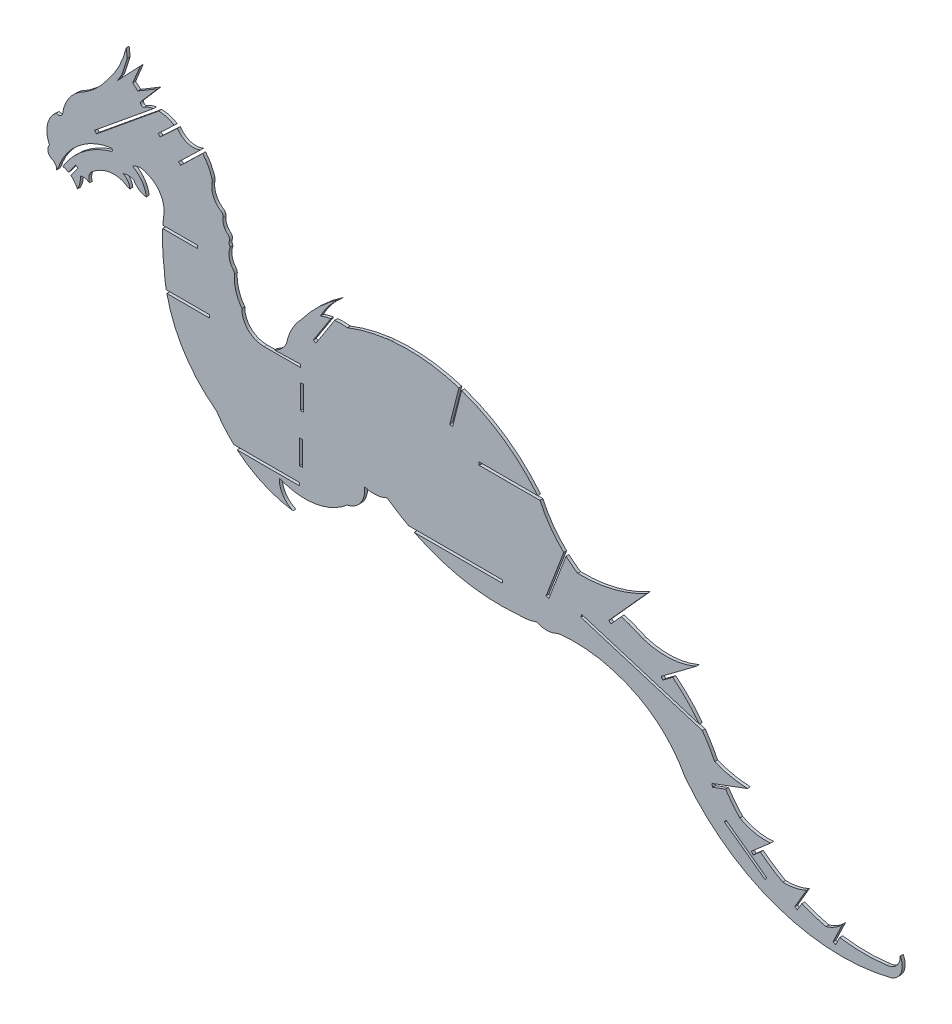
SolidWorks part; units mm, degrees
ref_plane "Front Plane" through (0, 0, 0) normal (0, 0, 1) x (1, 0, 0)
ref_plane "Top Plane" through (0, 0, 0) normal (0, 1, 0) x (1, 0, 0)
ref_plane "Right Plane" through (0, 0, 0) normal (1, 0, 0) x (0, 0, -1)
sketch "Sketch1" plane through (0, 0, 0) normal (0, 0, 1) x (1, 0, 0)
  line L13 (85.913, 218.9763) -> (74.3649, 207.8002)
  line L14 (84.8531, 220.0714) -> (73.305, 208.8953)
  line L15 (74.3649, 207.8002) -> (73.305, 208.8953)
  line L16 (72.6706, 223.8437) -> (63.5101, 215.2597)
  line L17 (70.9424, 224.3128) -> (62.468, 216.3718)
  line L18 (63.5101, 215.2597) -> (62.468, 216.3718)
  line L19 (53.5004, 226.3834) -> (62.3378, 236.6274)
  line L20 (71.6285, 224.9557) -> (62.468, 216.3718) construction
  line L21 (62.3378, 236.6274) -> (51.8511, 230.3661)
  line L22 (51.8511, 230.3661) -> (49.1514, 232.6951)
  line L23 (49.1514, 232.6951) -> (53.1855, 242.4071)
  line L24 (53.1855, 242.4071) -> (41.0252, 229.6436)
  line L25 (41.0252, 229.6436) -> (43.4334, 233.4967)
  line L26 (43.4334, 233.4967) -> (46.2631, 242.4071)
  line L27 (46.2631, 242.4071) -> (45.7814, 247.0429)
  line L33 (29.66, 200.589) -> (66.6896, 230.8776) construction
  line L49 (188.6151, 187.6952) -> (169.1948, 168.6314) construction
  line L51 (182.7923, 183.0471) -> (168.661, 169.1752)
  line L54 (185.2534, 183.3275) -> (169.7286, 168.0877)
  line L56 (168.661, 169.1752) -> (169.7286, 168.0877)
  line L57 (157.4617, 182.5358) -> (144.7171, 162.7649) construction
  line L58 (153.3021, 177.4895) -> (144.0766, 163.1777)
  line L59 (155.2936, 177.766) -> (145.3576, 162.352)
  line L60 (30.1424, 199.9991) -> (62.8231, 226.7305)
  line L61 (144.0766, 163.1777) -> (145.3576, 162.352)
  line L62 (188.0813, 188.239) -> (168.661, 169.1752) construction
  line L63 (158.1021, 182.123) -> (145.3576, 162.352) construction
  line L64 (156.8212, 182.9487) -> (144.0766, 163.1777) construction
  line L65 (189.1489, 187.1514) -> (169.7286, 168.0877) construction
  line L66 (29.1775, 201.1788) -> (60.1503, 226.5131)
  line L67 (30.1424, 199.9991) -> (29.1775, 201.1788)
  line L68 (30.1424, 199.9991) -> (67.1721, 230.2877) construction
  line L69 (29.1775, 201.1788) -> (66.2072, 231.4674) construction
  line L75 (16.6636, 174.3293) -> (20.4232, 179.4683)
  line L76 (15.3952, 175.1766) -> (19.1932, 180.3682)
  line L78 (20.4232, 179.4683) -> (19.1932, 180.3682)
  arc A0 (12.4112, 176.3386) -> (15.3952, 175.1766) centre (9.9945, 165.7194) cw
  arc A1 (20.0703, 169.8527) -> (21.6539, 176.5827) centre (9.8643, 175.8054) ccw
  arc A2 (21.6539, 176.5827) -> (26.4044, 175.8054) centre (23.3346, 171.949) cw
  arc A3 (26.4044, 175.8054) -> (27.2905, 181.1096) centre (31.4656, 177.686) cw
  arc A4 (27.2905, 181.1096) -> (35.949, 185.8295) centre (40.6259, 166.9481) cw
  arc A5 (35.949, 185.8295) -> (44.5288, 185.127) centre (39.1948, 172.7256) cw
  arc A6 (44.5288, 185.127) -> (47.6647, 183.6586) centre (51.8511, 196.6811) ccw
  arc A7 (47.6647, 183.6586) -> (44.1325, 188.8887) centre (41.5045, 183.3061) ccw
  arc A8 (44.1325, 188.8887) -> (49.7201, 188.8772) centre (46.9113, 181.6231) cw
  arc A9 (49.7201, 188.8772) -> (56.2646, 184.3098) centre (57.356, 192.8459) ccw
  arc A10 (56.2646, 184.3098) -> (49.1514, 194.7266) centre (42.906, 182.8248) ccw
  arc A11 (49.1514, 194.7266) -> (56.2715, 195.3335) centre (53.1855, 189.4687) cw
  arc A12 (56.2715, 195.3335) -> (65.6673, 182.2891) centre (52.257, 182.5358) cw
  arc A13 (65.6673, 182.2891) -> (65.646, 182.0044) centre (63.1277, 182.3359) cw
  arc A14 (65.7315, 155.9537) -> (70.314, 135.1914) centre (133.3951, 160.0009) ccw
  arc A15 (182.8341, 110.7237) -> (251.5533, 92.003) centre (242.2428, 193.3123) ccw
  arc A16 (161.9029, 96.9961) -> (163.2492, 97.3465) centre (159.7329, 108.0948) ccw
  arc A17 (170.8985, 109.8892) -> (182.8341, 110.7237) centre (175.8491, 124.8557) ccw
  arc A18 (445.4257, 29.3719) -> (452.4535, 37.0347) centre (444.9751, 36.8392) ccw
  arc A19 (452.4535, 37.0347) -> (447.9208, 24.8241) centre (444.8895, 32.896) cw
  arc A23 (261.361, 93.4868) -> (270.0689, 92.8939) centre (266.514, 104.9258) ccw
  arc A24 (272.556, 93.9304) -> (314.8204, 86.2928) centre (281.4797, 22.553) cw
  arc A25 (314.8204, 86.2928) -> (339.3161, 61.996) centre (287.7099, 34.4638) cw
  arc A26 (339.3161, 61.996) -> (447.9208, 24.8241) centre (421.7648, 125.6448) ccw
  arc A28 (445.4257, 29.3719) -> (361.4817, 65.9392) centre (433.7482, 117.1995) cw
  arc A29 (295.5346, 120.6114) -> (296.0785, 120.4577) centre (296.4931, 122.9637) ccw
  arc A30 (287.5207, 123.6481) -> (263.1364, 149.7627) centre (314.575, 173.3516) cw
  arc A31 (263.1364, 149.7627) -> (185.2534, 183.3275) centre (193.9218, 96.3002) ccw
  arc A32 (161.9029, 177.6862) -> (155.2936, 177.766) centre (158.253, 149.1443) ccw
  arc A33 (129.9784, 154.4832) -> (114.0338, 147.9574) centre (118.2489, 160.4005) cw
  arc A34 (114.0338, 147.9574) -> (106.5299, 158.7224) centre (117.5806, 158.4275) cw
  arc A35 (106.5299, 158.7224) -> (102.5636, 172.3071) centre (123.2009, 170.9612) cw
  arc A36 (101.9536, 174.13) -> (100.3802, 183.4958) centre (108.899, 180.1119) cw
  arc A37 (100.3802, 183.4958) -> (99.9418, 186.1014) centre (102.74, 185.2325) cw
  arc A38 (90.9092, 208.4497) -> (90.8696, 209.6659) centre (88.4246, 208.9777) ccw
  arc A39 (95.4624, 197.6442) -> (90.9092, 208.4497) centre (100.9454, 206.3167) cw
  arc A40 (90.8696, 209.6659) -> (85.913, 218.9763) centre (67.0577, 202.9636) ccw
  arc A41 (84.8531, 220.0714) -> (72.6706, 223.8437) centre (80.9007, 228.8651) cw
  arc A42 (70.9424, 224.3128) -> (62.8231, 226.7305) centre (62.7145, 211.5233) ccw
  arc A43 (55.5843, 224.9557) -> (53.5004, 226.3834) centre (54.5423, 225.6696) cw
  arc A44 (45.7814, 247.0429) -> (35.949, 227.5413) centre (-0.6105, 258.2036) cw
  arc A45 (35.949, 227.5413) -> (20.6241, 214.0554) centre (0.5756, 252.288) cw
  arc A46 (20.6241, 214.0554) -> (12.4112, 200.9147) centre (32.5604, 197.4584) ccw
  arc A47 (12.4112, 200.9147) -> (9.042, 198.9031) centre (10.1268, 200.9135) cw
  arc A48 (9.042, 198.9031) -> (5.4551, 182.6164) centre (17.1859, 188.5712) ccw
  arc A49 (5.4551, 182.6164) -> (7.0761, 176.5827) centre (8.3888, 180.1699) ccw
  arc A50 (7.0761, 176.5827) -> (9.1559, 173.0992) centre (5.7188, 173.4097) cw
  arc A51 (9.1559, 173.0992) -> (10.7671, 176.5827) centre (1.9369, 178.5526) ccw
  arc A52 (163.2492, 97.3465) -> (170.8985, 109.8892) centre (159.7329, 108.0948) ccw
  arc A53 (126.1618, 91.5175) -> (161.9029, 96.9961) centre (139.6981, 122.5329) ccw
  arc A54 (251.5533, 92.003) -> (261.361, 93.4868) centre (252.5143, 118.8054) ccw
  arc A55 (270.0689, 92.8939) -> (272.556, 93.9304) centre (266.514, 104.9258) ccw
  arc A56 (153.3021, 177.4895) -> (147.8071, 175.9555) centre (158.253, 149.1443) ccw
  arc A57 (182.7923, 183.0471) -> (161.9029, 177.6862) centre (193.9218, 96.3002) ccw
  arc A58 (10.7671, 176.5827) -> (37.5404, 197.4595) centre (43.0104, 162.8387) cw
  arc A59 (37.5404, 197.4595) -> (38.2537, 196.0719) centre (37.6686, 196.6483) cw
  arc A60 (38.2537, 196.0719) -> (12.4112, 176.3386) centre (50.3099, 153.495) ccw
  arc A61 (16.6636, 174.3293) -> (20.0703, 169.8527) centre (9.9945, 165.7194) cw
  arc A62 (65.646, 182.0044) -> (65.0583, 176.1999) centre (162.201, 169.2959) ccw
  arc A63 (64.9437, 164.2568) -> (65.7315, 155.9537) centre (162.201, 169.2959) ccw
  arc A64 (102.5636, 172.3071) -> (101.9536, 174.13) centre (100.029, 172.4724) ccw
  arc A65 (65.0583, 176.1999) -> (64.9437, 164.2568) centre (162.201, 169.2959) ccw
  arc A66 (99.9418, 186.1014) -> (99.1107, 188.8317) centre (97.516, 186.8546) ccw
  arc A67 (70.314, 135.1914) -> (73.526, 128.2136) centre (133.3951, 160.0009) ccw
  arc A68 (73.526, 128.2136) -> (78.3629, 120.4256) centre (133.3951, 160.0009) ccw
  arc A69 (78.3629, 120.4256) -> (86.4403, 111.1133) centre (133.3951, 160.0009) ccw
  arc A70 (86.4403, 111.1133) -> (93.1568, 105.4516) centre (133.3951, 160.0009) ccw
  arc A73 (295.5346, 120.6114) -> (287.9072, 123.4777) centre (239.5785, -16.7097) ccw
  arc A74 (287.9072, 123.4777) -> (287.5207, 123.6481) centre (288.735, 125.879) cw
  arc A75 (60.1503, 226.5131) -> (55.5843, 224.9557) centre (62.7145, 211.5233) ccw
  arc A76 (361.4817, 65.9392) -> (355.3136, 75.9918) centre (433.7482, 117.1995) cw
  arc A77 (137.7135, 169.2959) -> (158.253, 188.8317) centre (205.9089, 118.162) cw
  arc A78 (158.253, 188.8317) -> (147.8071, 175.9555) centre (185.6114, 155.9616) ccw
  arc A79 (99.1107, 188.8317) -> (96.6201, 195.1422) centre (103.4255, 194.1813) cw
  arc A80 (95.4624, 197.6442) -> (96.6201, 195.1422) centre (94.1051, 195.4973) cw
  arc A81 (296.0785, 120.4577) -> (355.3136, 75.9918) centre (282.9903, 41.3344) cw
  arc A82 (137.7135, 169.2959) -> (129.9784, 154.4832) centre (158.253, 149.1443) ccw
  arc A83 (93.1568, 105.4516) -> (133.3951, 80.0979) centre (141.151, 137.0147) ccw
  arc A84 (133.3951, 80.0979) -> (126.1618, 91.5175) centre (138.1529, 91.1122) cw
  point P60 (287.71, 123.5456)
  point P75 (106.4494, 191.8735)
  point P90 (91.9787, 207.5822)
  point P91 (85.8872, 203.0521)
  point P136 (164.6579, 97.7541)
  point P137 (151.9566, 109.3259)
  point P142 (123.8865, 90.8069)
  point P143 (131.5718, 107.0888)
  point P144 (122.5084, 91.4575)
  point P145 (130.1936, 107.7393)
  point P150 (241.3162, 93.1293)
  point P151 (251.1656, 111.671)
  point P152 (239.9703, 93.8443)
  point P153 (249.8198, 112.386)
  point P158 (270.5568, 91.3637)
  point P159 (265.469, 107.3203)
  point P160 (269.1048, 90.9007)
  point P161 (264.017, 106.8573)
  point P198 (15.578, 174.1358)
  point P199 (19.8082, 179.9183)
  point P200 (16.193, 173.6859)
  point P202 (14.963, 174.5857)
  point P210 (63.6959, 166.7845)
  point P211 (94.3235, 178.4306)
  point P231 (101.2609, 99.9132)
  point P232 (101.2609, 106.2632)
  point P235 (93.1199, 104.9862)
  point P236 (93.6225, 111.3162)
  point P239 (86.3932, 110.4968)
  point P240 (86.8776, 116.8283)
  point P243 (78.1854, 119.9829)
  point P244 (80.5491, 125.8766)
  point P247 (73.2876, 127.7593)
  point P248 (76.1666, 133.2444)
  point P251 (70.0194, 134.7217)
  point P252 (73.334, 140.0066)
  point P255 (67.1082, 144.2075)
  point P256 (71.8777, 148.3139)
  point P259 (66.0068, 151.6009)
  point P260 (70.2987, 156.2808)
  point P263 (65.3242, 160.5131)
  point P264 (71.0012, 163.5977)
  point P265 (64.2375, 165.36)
  point P266 (94.8652, 177.0061)
  point P267 (64.8673, 168.7878)
  point P268 (70.723, 171.6385)
  point P271 (64.7168, 175.6756)
  point P272 (70.283, 178.3947)
  point P275 (64.6704, 181.0332)
  point P276 (70.3416, 184.2665)
  point P301 (295.3884, 121.098)
  point P302 (295.0266, 120.6245)
  point P305 (305.7328, 115.9997)
  point P306 (434.7823, 117.834)
  point P307 (296.6449, 120.1538)
  point P308 (450.936, 28.713)
  point P309 (304.9899, 116.6907)
  point P310 (304.4572, 115.9935)
  point P311 (354.6735, 75.5721)
  point P312 (239.5785, -16.7097)
  point P313 (305.3928, 115.3177)
  point P314 (239.5785, -16.7097)
  point P327 (296.3516, 119.4504)
  point P328 (239.5785, -16.7097)
  point P329 (287.4626, 122.8248)
  point P330 (298.9702, 124.191)
  point P331 (294.7489, 119.0435)
  point P332 (309.5956, 122.086)
  point P333 (303.3169, 114.1841)
  point P334 (300.1486, 123.2246)
  point P335 (295.9273, 118.0771)
  point P336 (310.7887, 121.1379)
  point P337 (304.5101, 113.236)
  point P338 (323.9026, 122.7437)
  point P339 (308.7162, 107.8646)
  point P340 (336.2019, 120.1065)
  point P341 (320.6027, 104.9604)
  point P342 (352.8142, 116.9997)
  point P343 (330.7576, 95.3744)
  point P344 (364.3369, 112.5519)
  point P345 (337.296, 83.9421)
  point P346 (373.3591, 103.5516)
  point P347 (349.2999, 75.3797)
  point P348 (380.3752, 98.2442)
  point P349 (359.4005, 62.3807)
  point P350 (324.9692, 121.6551)
  point P351 (309.7827, 106.776)
  point P352 (337.2635, 119.0131)
  point P353 (321.6643, 103.867)
  point P354 (353.8812, 115.9115)
  point P355 (331.8246, 94.2862)
  point P356 (365.4445, 111.5051)
  point P357 (338.4036, 82.8953)
  point P358 (374.518, 102.5619)
  point P359 (350.4588, 74.39)
  point P360 (381.6907, 97.4748)
  point P361 (360.716, 61.6113)
  dimension "D18" = 2.54
  dimension "D19" = 2.54
  dimension "D20" = 2.54
  dimension "D21" = 2.54
  dimension "D4" = 2.54
  dimension "D22" = 2.54
  dimension "D2" = 1.524
  dimension "D3" = 1.524
  dimension "D12" = 0.762
  dimension "D13" = 0.762
  dimension "D14" = 0.762
  dimension "D15" = 0.762
  dimension "D16" = 0.762
  dimension "D17" = 0.762
extrude "Boss-Extrude1" add sketch "Sketch1" along normal blind 1.524
sketch "Sketch2" plane through (0, 0, 1.524) normal (0, 0, 1) x (1, 0, 0)
  line L0 (64.0284, 147.4046) -> (89.4284, 147.4046)
  line L1 (64.0284, 174.349) -> (83.0784, 174.349)
  line L2 (64.0284, 174.349) -> (64.0284, 175.873)
  line L3 (64.0284, 175.873) -> (83.0784, 175.873)
  line L4 (83.0784, 174.349) -> (83.0784, 175.873)
  line L5 (64.0284, 145.8806) -> (64.0284, 147.4046)
  line L6 (64.0284, 145.8806) -> (89.4284, 145.8806)
  line L7 (89.4284, 145.8806) -> (89.4284, 147.4046)
extrude "Cut-Extrude1" cut sketch "Sketch2" against normal blind 2.54
sketch "Sketch3" plane through (0, 0, 1.524) normal (0, 0, 1) x (1, 0, 0)
  line L0 (118.2489, 147.2629) -> (137.2989, 147.2629)
  line L1 (137.2989, 147.2629) -> (137.2989, 148.7869)
  line L2 (137.2989, 148.7869) -> (118.2489, 148.2418)
  line L3 (118.2489, 148.2418) -> (118.2489, 147.2629)
  line L4 (101.2252, 93.1675) -> (136.9055, 93.1675)
  line L5 (136.9055, 93.1675) -> (136.9055, 94.6915)
  line L6 (136.9055, 94.6915) -> (101.2252, 94.6915)
  line L7 (101.2252, 94.6915) -> (101.2252, 93.1675)
  line L9 (137.2989, 140.3932) -> (138.8229, 140.3932)
  line L10 (137.2989, 140.3932) -> (137.2989, 127.6932)
  line L11 (137.2989, 127.6932) -> (138.8229, 127.6932)
  line L12 (138.8229, 140.3932) -> (138.8229, 127.6932)
  line L13 (136.9055, 102.3186) -> (138.4295, 102.3186)
  line L14 (136.9055, 102.3186) -> (136.9055, 115.0186)
  line L15 (136.9055, 115.0186) -> (138.4295, 115.0186)
  line L16 (138.4295, 102.3186) -> (138.4295, 115.0186)
  dimension "D1" = 1.524
extrude "Cut-Extrude2" cut sketch "Sketch3" against normal blind 1.524
sketch "Sketch4" plane through (0, 0, 1.524) normal (0, 0, 1) x (1, 0, 0)
  line L1 (192.551, 103.6827) -> (243.351, 103.6827)
  line L2 (192.551, 103.6827) -> (192.551, 102.1587)
  line L3 (192.551, 102.1587) -> (243.351, 102.1587)
  line L4 (243.351, 103.6827) -> (243.351, 102.1587)
  line L5 (266.2542, 151.26) -> (231.2022, 151.26)
  line L6 (266.2542, 151.26) -> (266.2542, 149.736)
  line L7 (266.2542, 149.736) -> (231.2022, 149.736)
  line L8 (231.2022, 151.26) -> (231.2022, 149.736)
  dimension "D1" = 50.8
  dimension "D2" = 35.052
extrude "Cut-Extrude3" cut sketch "Sketch4" against normal blind 2.54
sketch "Sketch5" plane through (0, 0, 1.524) normal (0, 0, 1) x (1, 0, 0)
  line L5 (267.0948, 107.6519) -> (278.3494, 137.2694) construction
  line L6 (267.8071, 107.3813) -> (279.0617, 136.9987)
  line L7 (266.3825, 107.9226) -> (277.6371, 137.5401)
  line L8 (267.8071, 107.3813) -> (266.3825, 107.9226)
  line L9 (279.0617, 136.9987) -> (277.6371, 137.5401)
  dimension "D3" = 0.762
  dimension "D4" = 0.762
extrude "Cut-Extrude5" cut sketch "Sketch5" against normal blind 1.524
sketch "Sketch6" plane through (0, 0, 1.524) normal (0, 0, 1) x (1, 0, 0)
  line L0 (284.8664, 108.0438) -> (351.9145, 87.4136) construction
  line L1 (360.5306, 52.4382) -> (381.8587, 36.9499) construction
  line L2 (284.6423, 107.3155) -> (351.6904, 86.6853)
  line L3 (285.0905, 108.7721) -> (352.1386, 88.1419)
  line L4 (284.6423, 107.3155) -> (285.0905, 108.7721)
  line L5 (351.6904, 86.6853) -> (352.1386, 88.1419)
  line L6 (360.0828, 51.8216) -> (381.411, 36.3333)
  line L7 (360.9783, 53.0548) -> (382.3065, 37.5665)
  line L8 (360.0828, 51.8216) -> (360.9783, 53.0548)
  line L9 (381.411, 36.3333) -> (382.3065, 37.5665)
  dimension "D1" = 0.762
  dimension "D2" = 0.762
  dimension "D3" = 0.762
  dimension "D4" = 0.762
extrude "Cut-Extrude6" cut sketch "Sketch6" against normal blind 1.524
sketch "Sketch7" plane through (0, 0, 1.524) normal (0, 0, 1) x (1, 0, 0)
  line L0 (319.4926, 135.606) -> (302.3185, 116.5409)
  line L1 (345.278, 115.2927) -> (329.3189, 103.3316)
  line L2 (372.1628, 73.1128) -> (357.5519, 67.6213)
  line L3 (384.3276, 54.3867) -> (376.0505, 47.1527)
  line L4 (403.1844, 42.2982) -> (398.8415, 34.8569)
  line L5 (422.1839, 36.4052) -> (418.5463, 28.7852)
  arc A0 (282.9076, 126.4522) -> (319.4926, 135.606) centre (284.4269, 198.0669) ccw
  arc A1 (352.9687, 77.5443) -> (372.1628, 73.1128) centre (374.3704, 126.4584) ccw
  arc A4 (357.5519, 67.6213) -> (352.9687, 77.5443) centre (377.8557, 83.0192) cw
  arc A5 (302.3185, 116.5409) -> (282.9076, 126.4522) centre (301.3022, 138.5137) cw
  arc A6 (317.322, 113.8129) -> (345.278, 115.2927) centre (329.3516, 151.3629) ccw
  arc A8 (317.322, 113.8129) -> (329.3189, 103.3316) centre (287.5429, 67.6213) cw
  arc A9 (276.8479, 131.1729) -> (287.5207, 123.6481) centre (314.575, 173.3516) ccw construction
  arc A10 (346.9297, 89.7446) -> (296.0785, 120.4577) centre (282.9903, 41.3344) ccw construction
  arc A11 (368.1075, 57.6902) -> (384.3276, 54.3867) centre (381.6349, 82.6377) ccw
  arc A12 (355.3136, 75.9918) -> (445.4257, 29.3719) centre (433.7482, 117.1995) ccw construction
  arc A14 (376.0505, 47.1527) -> (368.1075, 57.6902) centre (384.3482, 61.6699) cw
  arc A15 (388.8954, 39.8631) -> (403.1844, 42.2982) centre (391.4453, 68.0409) ccw
  arc A17 (388.8954, 39.8631) -> (398.8415, 34.8569) centre (398.8149, 47.1876) ccw
  arc A18 (411.4838, 30.4758) -> (422.1839, 36.4052) centre (408.2212, 48.9826) ccw
  arc A20 (418.5463, 28.7852) -> (411.4838, 30.4758) centre (416.6369, 36.4052) cw
extrude "Boss-Extrude3" add sketch "Sketch7" against normal blind 1.524
sketch "Sketch11" plane through (0, 0, 1.524) normal (0, 0, 1) x (1, 0, 0)
  line L0 (304.6437, 119.1221) -> (299.3049, 113.1955)
  line L2 (299.3049, 113.1955) -> (300.4373, 112.1755)
  line L3 (300.4373, 112.1755) -> (306.2858, 118.668)
  line L4 (306.2858, 118.668) -> (304.6437, 119.1221)
  line L5 (332.425, 105.6596) -> (326.7999, 101.4436)
  line L6 (326.7999, 101.4436) -> (327.7139, 100.2241)
  line L7 (327.7139, 100.2241) -> (333.671, 104.6888)
  line L8 (333.671, 104.6888) -> (332.425, 105.6596)
  line L9 (362.9926, 69.6662) -> (353.3742, 66.0511)
  line L10 (353.3742, 66.0511) -> (353.9374, 64.5527)
  line L11 (353.9374, 64.5527) -> (363.7622, 68.2454)
  line L12 (363.7622, 68.2454) -> (362.9926, 69.6662)
  line L13 (359.7632, 68.4524) -> (372.1628, 73.1128) construction
  line L14 (379.65, 50.2986) -> (374.2601, 45.5919)
  line L15 (377.6914, 48.5868) -> (384.3276, 54.3867) construction
  line L16 (374.2601, 45.5919) -> (375.2625, 44.444)
  line L17 (375.2625, 44.444) -> (380.6525, 49.1507)
  line L18 (380.6525, 49.1507) -> (379.65, 50.2986)
  line L19 (400.3665, 37.4699) -> (397.0371, 31.7652)
  line L20 (399.266, 35.5843) -> (403.1844, 42.2982) construction
  line L21 (397.0371, 31.7652) -> (398.3533, 30.997)
  line L22 (398.3533, 30.997) -> (401.6827, 36.7017)
  line L23 (401.6827, 36.7017) -> (400.3665, 37.4699)
  line L24 (419.8219, 31.4573) -> (417.1491, 25.8583)
  line L25 (419.044, 29.8276) -> (422.1839, 36.4052) construction
  line L26 (417.1491, 25.8583) -> (418.5245, 25.2017)
  line L27 (418.5245, 25.2017) -> (421.2909, 30.997)
  line L28 (421.2909, 30.997) -> (419.8219, 31.4573)
extrude "Cut-Extrude11" cut sketch "Sketch11" against normal blind 1.524 contours L3 L4 L0 L2 | L7 L8 L5 L6 | L11 L12 L9 L10 | L17 L18 L14 L16 | L22 L23 L19 L21 | L27 L28 L24 L26
sketch "Sketch12" plane through (0, 0, 1.524) normal (0, 0, 1) x (1, 0, 0)
  line L0 (182.7923, 183.0471) -> (168.661, 169.1752)
  line L1 (168.661, 169.1752) -> (169.7286, 168.0877)
  line L2 (169.7286, 168.0877) -> (185.2534, 183.3275)
  arc A0 (182.7923, 183.0471) -> (185.2534, 183.3275) centre (185.5897, 169.4345) cw
extrude "Boss-Extrude4" add sketch "Sketch12" against normal blind 1.524
sketch "Sketch13" plane through (0, 0, 0) normal (0, 0, -1) x (-1, 0, 0)
  line L0 (-215.7479, 160.6303) -> (-221.2765, 182.535)
  line L1 (-217.2256, 160.2573) -> (-222.7542, 182.162)
  line L2 (-216.4868, 160.4438) -> (-222.0153, 182.3485) construction
  line L3 (-215.7479, 160.6303) -> (-217.2256, 160.2573)
  line L4 (-221.2765, 182.535) -> (-222.7542, 182.162)
  dimension "D1" = 0.762
  dimension "D2" = 0.762
extrude "Cut-Extrude12" cut sketch "Sketch13" against normal blind 1.524
